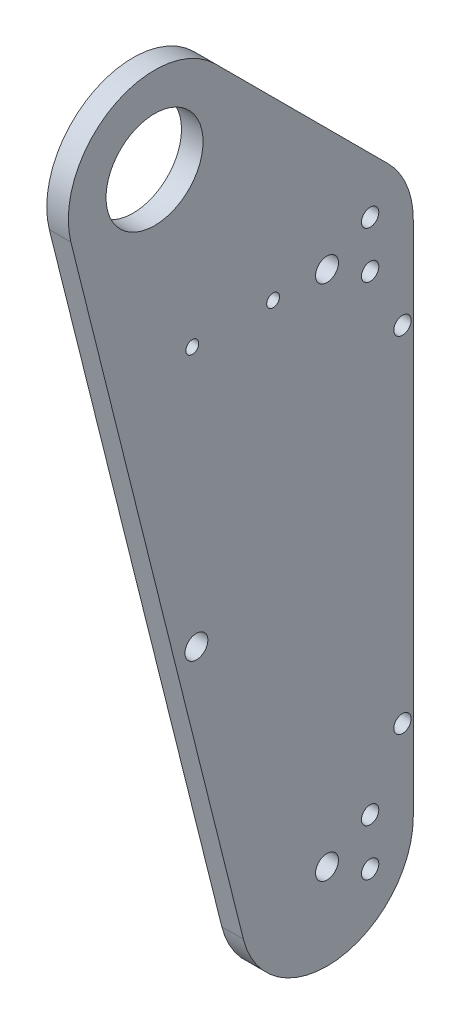
SolidWorks part; units mm, degrees
material "6061-T6 (SS)"
ref_plane "Front Plane" through (0, 0, 0) normal (0, 0, 1) x (1, 0, 0)
ref_plane "Top Plane" through (0, 0, 0) normal (0, 1, 0) x (1, 0, 0)
ref_plane "Right Plane" through (0, 0, 0) normal (1, 0, 0) x (0, 0, -1)
sketch "SkeletonSketch" plane through (0, 0, 0) normal (1, 0, 0) x (0, 0, -1)
  line L0 (50.8, -50.8) -> (50.8, -203.2) construction
  line L1 (34.925, -50.8) -> (11.1125, -50.8) construction
  line L2 (0, 0) -> (50.8, -203.2) construction
  line L3 (30.802, -123.2081) -> (12.3208, -127.8284) construction
  line L4 (50.8, -76.2) -> (73.025, -76.2) construction
  line L5 (73.025, -177.8) -> (73.025, -76.2) construction
  point P0 (50.8, -50.8)
  point P1 (50.8, -203.2)
  point P2 (0, 0)
  point P15 (0, 0)
  dimension "D1" = 152.4
  dimension "D2" = 50.8
  dimension "D3" = 50.8
  dimension "D4" = 25.4
  dimension "D6" = 23.8125
  dimension "D7" = 15.875
  dimension "D8" = 127
  dimension "D9" = 19.05
  dimension "D10" = 22.225
  dimension "D11" = 101.6
sketch "Sketch2" plane through (0, 0, 0) normal (1, 0, 0) x (0, 0, -1)
  line L0 (68.7605, -32.8395) -> (17.9605, 17.9605)
  line L1 (-24.6416, -6.1604) -> (26.1584, -209.3604)
  line L2 (76.2, -203.2) -> (76.2, -50.8)
  arc A0 (17.9605, 17.9605) -> (-24.6416, -6.1604) centre (0, 0) ccw
  arc A1 (76.2, -50.8) -> (68.7605, -32.8395) centre (50.8, -50.8) ccw
  arc A2 (26.1584, -209.3604) -> (76.2, -203.2) centre (50.8, -203.2) ccw
  dimension "D1" = 25.4
extrude "Boss-Extrude1" add sketch "Sketch2" along normal blind 6.35
hole_wizard "1 (1) Diameter Hole1" positions "Sketch3" profile "Sketch4" hole size "1" standard "ANSI Inch" end condition through all
sketch "Sketch3" plane through (6.35, 0, 0) normal (1, 0, 0) x (0, 0, -1)
  point P0 (0, 0)
sketch "Sketch4" plane through (6.35, 0, 0) normal (0, 1, 0) x (0, 0, -1)
  line L0 (0, 0) -> (0, 6.35)
  line L1 (0, 6.35) -> (14.2875, 6.35)
  line L2 (14.2875, 6.35) -> (14.2875, 0)
  line L5 (14.2875, 0) -> (0, 0)
  line L11 (0, -6.35) -> (0, 107.95) construction
  dimension "Thru Hole Dia." = 28.575
  dimension "Thru Hole Depth" = 6.35
hole_wizard "1/4 Clearance Hole1" positions "Sketch7" profile "Sketch8" hole size "1/4" standard "ANSI Inch" end condition through all
sketch "Sketch7" plane through (6.35, 0, 0) normal (1, 0, 0) x (0, 0, -1)
  point P12 (50.8, -50.8)
  point P15 (50.8, -203.2)
  point P41 (12.3208, -127.8284)
sketch "Sketch8" plane through (6.35, -50.8, -50.8) normal (0, 1, 0) x (0, 0, -1)
  line L0 (0, 0) -> (0, 6.35)
  line L1 (0, 6.35) -> (3.3782, 6.35)
  line L2 (3.3782, 6.35) -> (3.3782, 0)
  line L5 (3.3782, 0) -> (0, 0)
  line L11 (0, -6.35) -> (0, 107.95) construction
  dimension "Thru Hole Dia." = 6.7564
  dimension "Thru Hole Depth" = 6.35
hole_wizard "1/4-20 Tapped Hole1" positions "Sketch9" profile "Sketch10" tap size "1/4-20" standard "ANSI Inch" end condition through all
sketch "Sketch9" plane through (0, 0, 0) normal (-1, 0, 0) x (0, 0, 1)
  line L0 (-63.5, -43.8912) -> (-63.5, -57.7088) construction
  line L3 (-63.5, -210.1088) -> (-63.5, -196.2912) construction
  point P0 (-63.5, -57.7088)
  point P2 (-63.5, -43.8912)
  point P4 (-63.5, -196.2912)
  point P6 (-63.5, -210.1088)
  point P41 (-63.5, -50.8)
  point P46 (-63.5, -203.2)
  dimension "D2" = 13.8176
  dimension "D4" = 13.8176
  dimension "D1" = 12.7
  dimension "D3" = 12.7
sketch "Sketch10" plane through (0, -57.7088, -63.5) normal (0, 1, 0) x (0, 0, 1)
  line L0 (0, 0) -> (0, 6.35)
  line L1 (0, 6.35) -> (2.5527, 6.35)
  line L2 (2.5527, 6.35) -> (2.5527, 0)
  line L5 (2.5527, 0) -> (0, 0)
  line L11 (0, -6.35) -> (0, 107.95) construction
  dimension "Thru Tap Drill Dia." = 5.1054
  dimension "Thru Tap Drill Depth" = 6.35
cosmetic thread "Hole Thread1"
cosmetic thread "Hole Thread2"
cosmetic thread "Hole Thread3"
cosmetic thread "Hole Thread4"
hole_wizard "#10-24 Tapped Hole1" positions "Sketch11" profile "Sketch12" tap size "#10-24" standard "ANSI Inch" end condition through all
sketch "Sketch11" plane through (0, 0, 0) normal (-1, 0, 0) x (0, 0, 1)
  point P0 (-34.925, -50.8)
  point P3 (-11.1125, -50.8)
sketch "Sketch12" plane through (0, -50.8, -34.925) normal (0, 1, 0) x (0, 0, 1)
  line L0 (0, 0) -> (0, 6.35)
  line L1 (0, 6.35) -> (1.8986, 6.35)
  line L2 (1.8986, 6.35) -> (1.8986, 0)
  line L5 (1.8986, 0) -> (0, 0)
  line L11 (0, -6.35) -> (0, 107.95) construction
  dimension "Thru Tap Drill Dia." = 3.7973
  dimension "Thru Tap Drill Depth" = 6.35
cosmetic thread "Hole Thread5"
cosmetic thread "Hole Thread6"
hole_wizard "#10 Clearance Hole1" positions "Sketch13" profile "Sketch14" hole size "#10" standard "ANSI Inch" end condition through all
sketch "Sketch13" plane through (0, 0, 0) normal (-1, 0, 0) x (0, 0, 1)
  point P0 (-73.025, -76.2)
  point P3 (-73.025, -177.8)
sketch "Sketch14" plane through (0, -76.2, -73.025) normal (0, 1, 0) x (0, 0, 1)
  line L0 (0, 0) -> (0, 6.35)
  line L1 (0, 6.35) -> (2.5527, 6.35)
  line L2 (2.5527, 6.35) -> (2.5527, 0)
  line L5 (2.5527, 0) -> (0, 0)
  line L11 (0, -6.35) -> (0, 107.95) construction
  dimension "Thru Hole Dia." = 5.1054
  dimension "Thru Hole Depth" = 6.35
equation "\"D3@Sketch9\"=\"D1@Sketch9\""
